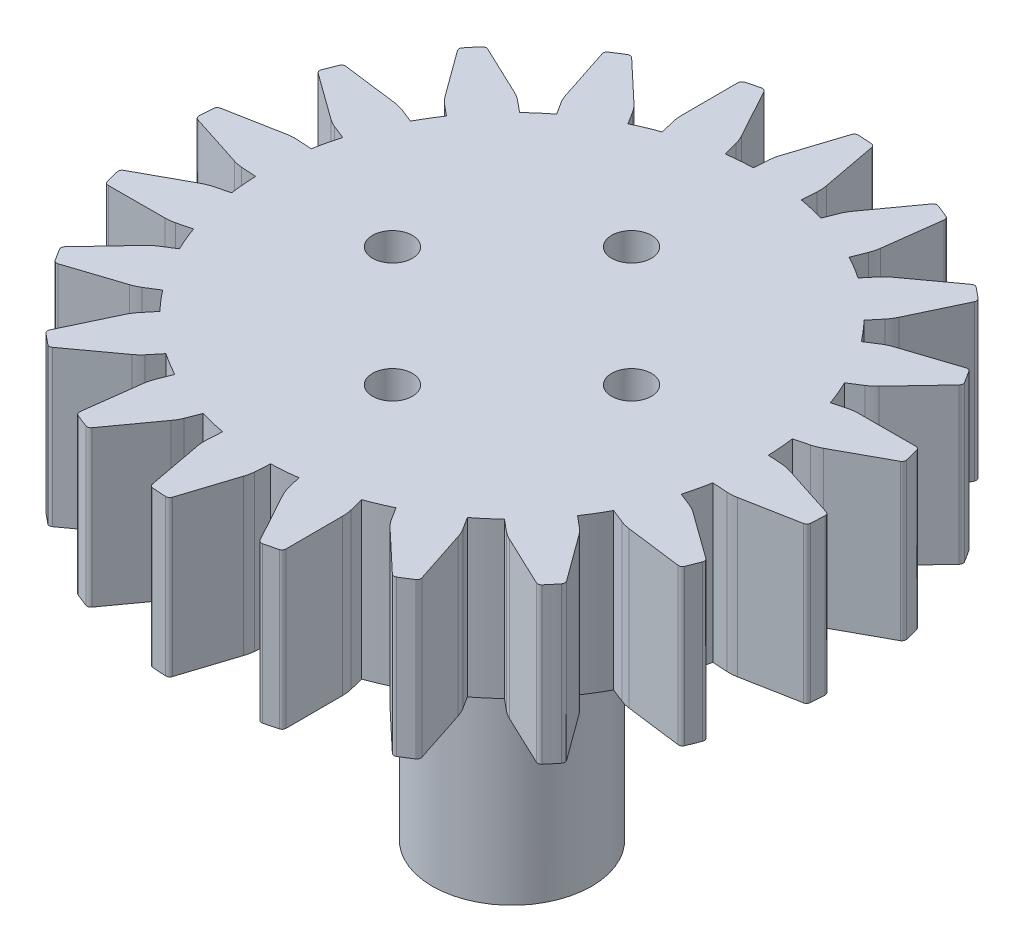
SolidWorks part; units mm, degrees
ref_plane "Front Plane" through (0, 0, 0) normal (0, 0, 1) x (1, 0, 0)
ref_plane "Top Plane" through (0, 0, 0) normal (0, 1, 0) x (1, 0, 0)
ref_plane "Right Plane" through (0, 0, 0) normal (1, 0, 0) x (0, 0, -1)
sketch "Sketch1" plane through (0, 0, 0) normal (0, 1, 0) x (1, 0, 0)
  line L1 (2.0673, 12.6488) -> (2.1144, 13.3972)
  line L2 (2.0838, 13.8927) -> (1.5574, 16.6892)
  line L3 (0.4846, 16.7567) -> (-0.3881, 14.0482)
  line L4 (-0.4814, 13.5905) -> (-0.5285, 12.8421)
  line L11 (5.7598, 11.3604) -> (6.0358, 12.0576)
  line L12 (6.1599, 12.5383) -> (6.5234, 15.3605)
  line L13 (5.524, 15.7563) -> (3.8571, 13.4501)
  line L14 (3.6268, 13.0436) -> (3.3508, 12.3464)
  line L15 (8.8735, 8.994) -> (9.3514, 9.5718)
  line L16 (9.618, 9.9906) -> (10.8358, 12.5624)
  line L17 (10.0076, 13.2476) -> (7.7096, 11.5694)
  line L18 (7.365, 11.2539) -> (6.8871, 10.6762)
  line L19 (11.1035, 5.7812) -> (11.7366, 6.183)
  line L20 (12.1195, 6.499) -> (14.0725, 8.5686)
  line L21 (13.4965, 9.4762) -> (10.7924, 8.5902)
  line L22 (10.3672, 8.3967) -> (9.7341, 7.9949)
  line L23 (12.2315, 2.0366) -> (12.9578, 2.2231)
  line L24 (13.4196, 2.4053) -> (15.9166, 3.77)
  line L25 (15.6492, 4.8112) -> (12.8037, 4.8042)
  line L26 (12.3395, 4.7515) -> (11.6132, 4.5651)
  line L27 (12.1472, -1.8734) -> (12.8956, -1.9204)
  line L28 (13.3911, -1.8899) -> (16.1876, -1.3635)
  line L29 (16.2551, -0.2907) -> (13.5466, 0.582)
  line L30 (13.0889, 0.6753) -> (12.3405, 0.7224)
  line L31 (10.8588, -5.5659) -> (11.556, -5.8419)
  line L32 (12.0367, -5.966) -> (14.8589, -6.3295)
  line L33 (15.2546, -5.3301) -> (12.9485, -3.6631)
  line L34 (12.542, -3.4329) -> (11.8448, -3.1569)
  line L35 (8.4924, -8.6796) -> (9.0702, -9.1575)
  line L36 (9.489, -9.424) -> (12.0608, -10.6419)
  line L37 (12.746, -9.8137) -> (11.0678, -7.5157)
  line L38 (10.7523, -7.1711) -> (10.1745, -6.6931)
  line L39 (5.2796, -10.9096) -> (5.6814, -11.5427)
  line L40 (5.9974, -11.9256) -> (8.0669, -13.8786)
  line L41 (8.9745, -13.3026) -> (8.0886, -10.5985)
  line L42 (7.8951, -10.1733) -> (7.4933, -9.5402)
  line L43 (1.535, -12.0376) -> (1.7215, -12.7639)
  line L44 (1.9037, -13.2257) -> (3.2684, -15.7226)
  line L45 (4.3096, -15.4553) -> (4.3026, -12.6098)
  line L46 (4.2499, -12.1456) -> (4.0635, -11.4193)
  line L47 (-2.375, -11.9533) -> (-2.422, -12.7017)
  line L48 (-2.3915, -13.1972) -> (-1.8651, -15.9936)
  line L49 (-0.7923, -16.0611) -> (0.0804, -13.3527)
  line L50 (0.1737, -12.895) -> (0.2208, -12.1466)
  line L51 (-6.0675, -10.6649) -> (-6.3435, -11.3621)
  line L52 (-6.4676, -11.8428) -> (-6.8311, -14.665)
  line L53 (-5.8317, -15.0607) -> (-4.1648, -12.7546)
  line L54 (-3.9345, -12.348) -> (-3.6585, -11.6509)
  line L55 (-9.1812, -8.2985) -> (-9.6591, -8.8762)
  line L56 (-9.9257, -9.2951) -> (-11.1435, -11.8668)
  line L57 (-10.3153, -12.552) -> (-8.0173, -10.8738)
  line L58 (-7.6727, -10.5584) -> (-7.1948, -9.9806)
  line L59 (-11.4112, -5.0857) -> (-12.0443, -5.4875)
  line L60 (-12.4272, -5.8035) -> (-14.3802, -7.873)
  line L61 (-13.8042, -8.7806) -> (-11.1001, -7.8947)
  line L62 (-10.6749, -7.7011) -> (-10.0418, -7.2994)
  line L63 (-12.5392, -1.3411) -> (-13.2655, -1.5275)
  line L64 (-13.7273, -1.7097) -> (-16.2243, -3.0745)
  line L65 (-15.9569, -4.1157) -> (-13.1114, -4.1087)
  line L66 (-12.6472, -4.056) -> (-11.9209, -3.8695)
  line L67 (-12.4549, 2.5689) -> (-13.2033, 2.616)
  line L68 (-13.6988, 2.5854) -> (-16.4952, 2.059)
  line L69 (-16.5627, 0.9862) -> (-13.8543, 0.1135)
  line L70 (-13.3966, 0.0202) -> (-12.6482, -0.0269)
  line L71 (-11.1665, 6.2614) -> (-11.8637, 6.5374)
  line L72 (-12.3444, 6.6615) -> (-15.1666, 7.0251)
  line L73 (-15.5623, 6.0256) -> (-13.2562, 4.3587)
  line L74 (-12.8497, 4.1285) -> (-12.1525, 3.8524)
  line L75 (-8.8001, 9.3751) -> (-9.3778, 9.853)
  line L76 (-9.7967, 10.1196) -> (-12.3685, 11.3374)
  line L77 (-13.0536, 10.5092) -> (-11.3754, 8.2112)
  line L78 (-11.06, 7.8666) -> (-10.4822, 7.3887)
  line L79 (-5.5873, 11.6051) -> (-5.9891, 12.2382)
  line L80 (-6.3051, 12.6211) -> (-8.3746, 14.5741)
  line L81 (-9.2822, 13.9981) -> (-8.3963, 11.294)
  line L82 (-8.2027, 10.8688) -> (-7.801, 10.2357)
  line L83 (-1.8427, 12.7332) -> (-2.0292, 13.4594)
  line L84 (-2.2114, 13.9213) -> (-3.5761, 16.4182)
  line L85 (-4.6173, 16.1508) -> (-4.6103, 13.3053)
  line L86 (-4.5576, 12.8411) -> (-4.3711, 12.1149)
  arc A1 (3.3508, 12.3464) -> (2.0673, 12.6488) centre (-0.1538, 0.3478) ccw
  arc A2 (-0.5285, 12.8421) -> (-1.8427, 12.7332) centre (-0.1538, 0.3478) ccw
  arc A3 (2.1144, 13.3972) -> (2.0838, 13.8927) centre (0.1183, 13.5228) ccw
  arc A4 (1.5574, 16.6892) -> (1.3769, 16.8515) centre (1.3609, 16.6522) ccw
  arc A5 (1.3769, 16.8515) -> (0.684, 16.8951) centre (-0.2094, -2.8347) ccw
  arc A6 (0.684, 16.8951) -> (0.4846, 16.7567) centre (0.675, 16.6953) ccw
  arc A7 (-0.3881, 14.0482) -> (-0.4814, 13.5905) centre (1.5115, 13.4225) ccw
  arc A8 (-4.3711, 12.1149) -> (-5.5873, 11.6051) centre (-0.1538, 0.3478) ccw
  arc A9 (-7.801, 10.2357) -> (-8.8001, 9.3751) centre (-0.1538, 0.3478) ccw
  arc A10 (-10.4822, 7.3887) -> (-11.1665, 6.2614) centre (-0.1538, 0.3478) ccw
  arc A11 (-12.1525, 3.8524) -> (-12.4549, 2.5689) centre (-0.1538, 0.3478) ccw
  arc A12 (-12.6482, -0.0269) -> (-12.5392, -1.3411) centre (-0.1538, 0.3478) ccw
  arc A14 (-11.9209, -3.8695) -> (-11.4112, -5.0857) centre (-0.1538, 0.3478) ccw
  arc A15 (-10.0418, -7.2994) -> (-9.1812, -8.2985) centre (-0.1538, 0.3478) ccw
  arc A16 (-7.1948, -9.9806) -> (-6.0675, -10.6649) centre (-0.1538, 0.3478) ccw
  arc A17 (-3.6585, -11.6509) -> (-2.375, -11.9533) centre (-0.1538, 0.3478) ccw
  arc A18 (0.2208, -12.1466) -> (1.535, -12.0376) centre (-0.1538, 0.3478) ccw
  arc A19 (6.0358, 12.0576) -> (6.1599, 12.5383) centre (4.1763, 12.7938) ccw
  arc A20 (6.5234, 15.3605) -> (6.402, 15.5707) centre (6.3251, 15.3861) ccw
  arc A21 (6.402, 15.5707) -> (5.7564, 15.8263) centre (-1.1901, -2.6617) ccw
  arc A22 (5.7564, 15.8263) -> (5.524, 15.7563) centre (5.6861, 15.6391) ccw
  arc A23 (3.8571, 13.4501) -> (3.6268, 13.0436) centre (5.4703, 12.268) ccw
  arc A24 (9.3514, 9.5718) -> (9.618, 9.9906) centre (7.8104, 10.8466) ccw
  arc A25 (10.8358, 12.5624) -> (10.7853, 12.7998) centre (10.6551, 12.648) ccw
  arc A26 (10.7853, 12.7998) -> (10.2503, 13.2424) centre (-2.0694, -2.1942) ccw
  arc A27 (10.2503, 13.2424) -> (10.0076, 13.2476) centre (10.1255, 13.0861) ccw
  arc A28 (7.7096, 11.5694) -> (7.365, 11.2539) centre (8.8786, 9.9466) ccw
  arc A29 (11.7366, 6.183) -> (12.1195, 6.499) centre (10.6649, 7.8717) ccw
  arc A30 (14.0725, 8.5686) -> (14.0978, 8.81) centre (13.927, 8.7058) ccw
  arc A31 (14.0978, 8.81) -> (13.7257, 9.3962) centre (-2.7612, -1.4778) ccw
  arc A32 (13.7257, 9.3962) -> (13.4965, 9.4762) centre (13.5588, 9.2861) ccw
  arc A33 (10.7924, 8.5902) -> (10.3672, 8.3967) centre (11.4027, 6.6856) ccw
  arc A34 (12.9578, 2.2231) -> (13.4196, 2.4053) centre (12.4604, 4.1602) ccw
  arc A35 (15.9166, 3.77) -> (16.0152, 3.9918) centre (15.8206, 3.9455) ccw
  arc A36 (16.0152, 3.9918) -> (15.8425, 4.6643) centre (-3.1977, -0.5828) ccw
  arc A37 (15.8425, 4.6643) -> (15.6492, 4.8112) centre (15.6497, 4.6112) ccw
  arc A38 (12.8037, 4.8042) -> (12.3395, 4.7515) centre (12.7956, 2.8042) ccw
  arc A39 (12.8956, -1.9204) -> (13.3911, -1.8899) centre (13.0212, 0.0756) ccw
  arc A40 (16.1876, -1.3635) -> (16.3499, -1.183) centre (16.1506, -1.167) ccw
  arc A41 (16.3499, -1.183) -> (16.3935, -0.4901) centre (-3.3363, 0.4034) ccw
  arc A42 (16.3935, -0.4901) -> (16.2551, -0.2907) centre (16.1937, -0.4811) ccw
  arc A43 (13.5466, 0.582) -> (13.0889, 0.6753) centre (12.9209, -1.3176) ccw
  arc A44 (11.556, -5.8419) -> (12.0367, -5.966) centre (12.2922, -3.9824) ccw
  arc A45 (14.8589, -6.3295) -> (15.0691, -6.208) centre (14.8845, -6.1312) ccw
  arc A46 (15.0691, -6.208) -> (15.3247, -5.5625) centre (-3.1633, 1.3841) ccw
  arc A47 (15.3247, -5.5625) -> (15.2546, -5.3301) centre (15.1375, -5.4922) ccw
  arc A48 (12.9485, -3.6631) -> (12.542, -3.4329) centre (11.7664, -5.2764) ccw
  arc A49 (9.0702, -9.1575) -> (9.489, -9.424) centre (10.345, -7.6165) ccw
  arc A50 (12.0608, -10.6419) -> (12.2982, -10.5913) centre (12.1464, -10.4612) ccw
  arc A51 (12.2982, -10.5913) -> (12.7408, -10.0564) centre (-2.6958, 2.2633) ccw
  arc A52 (12.7408, -10.0564) -> (12.746, -9.8137) centre (12.5844, -9.9316) ccw
  arc A53 (11.0678, -7.5157) -> (10.7523, -7.1711) centre (9.445, -8.6847) ccw
  arc A54 (5.6814, -11.5427) -> (5.9974, -11.9256) centre (7.3701, -10.471) ccw
  arc A55 (8.0669, -13.8786) -> (8.3084, -13.9038) centre (8.2042, -13.7331) ccw
  arc A56 (8.3084, -13.9038) -> (8.8946, -13.5318) centre (-1.9795, 2.9551) ccw
  arc A57 (8.8946, -13.5318) -> (8.9745, -13.3026) centre (8.7845, -13.3649) ccw
  arc A58 (8.0886, -10.5985) -> (7.8951, -10.1733) centre (6.184, -11.2088) ccw
  arc A59 (1.7215, -12.7639) -> (1.9037, -13.2257) centre (3.6586, -12.2665) ccw
  arc A60 (3.2684, -15.7226) -> (3.4902, -15.8213) centre (3.4439, -15.6267) ccw
  arc A61 (3.4902, -15.8213) -> (4.1627, -15.6486) centre (-1.0844, 3.3916) ccw
  arc A62 (4.1627, -15.6486) -> (4.3096, -15.4553) centre (4.1096, -15.4558) ccw
  arc A63 (4.3026, -12.6098) -> (4.2499, -12.1456) centre (2.3026, -12.6017) ccw
  arc A64 (-2.422, -12.7017) -> (-2.3915, -13.1972) centre (-0.426, -12.8272) ccw
  arc A65 (-1.8651, -15.9936) -> (-1.6846, -16.156) centre (-1.6686, -15.9566) ccw
  arc A66 (-1.6846, -16.156) -> (-0.9917, -16.1996) centre (-0.0982, 3.5302) ccw
  arc A67 (-0.9917, -16.1996) -> (-0.7923, -16.0611) centre (-0.9827, -15.9998) ccw
  arc A68 (0.0804, -13.3527) -> (0.1737, -12.895) centre (-1.8192, -12.727) ccw
  arc A69 (-6.3435, -11.3621) -> (-6.4676, -11.8428) centre (-4.484, -12.0983) ccw
  arc A70 (-6.8311, -14.665) -> (-6.7097, -14.8752) centre (-6.6328, -14.6906) ccw
  arc A71 (-6.7097, -14.8752) -> (-6.0641, -15.1308) centre (0.8825, 3.3573) ccw
  arc A72 (-6.0641, -15.1308) -> (-5.8317, -15.0607) centre (-5.9938, -14.9436) ccw
  arc A73 (-4.1648, -12.7546) -> (-3.9345, -12.348) centre (-5.778, -11.5725) ccw
  arc A74 (-9.6591, -8.8762) -> (-9.9257, -9.2951) centre (-8.1181, -10.1511) ccw
  arc A75 (-11.1435, -11.8668) -> (-11.0929, -12.1043) centre (-10.9628, -11.9524) ccw
  arc A76 (-11.0929, -12.1043) -> (-10.558, -12.5468) centre (1.7617, 2.8897) ccw
  arc A77 (-10.558, -12.5468) -> (-10.3153, -12.552) centre (-10.4332, -12.3905) ccw
  arc A78 (-8.0173, -10.8738) -> (-7.6727, -10.5584) centre (-9.1863, -9.2511) ccw
  arc A79 (-12.0443, -5.4875) -> (-12.4272, -5.8035) centre (-10.9726, -7.1761) ccw
  arc A80 (-14.3802, -7.873) -> (-14.4054, -8.1145) centre (-14.2347, -8.0103) ccw
  arc A81 (-14.4054, -8.1145) -> (-14.0334, -8.7007) centre (2.4535, 2.1734) ccw
  arc A82 (-14.0334, -8.7007) -> (-13.8042, -8.7806) centre (-13.8665, -8.5906) ccw
  arc A83 (-11.1001, -7.8947) -> (-10.6749, -7.7011) centre (-11.7104, -5.9901) ccw
  arc A84 (-13.2655, -1.5275) -> (-13.7273, -1.7097) centre (-12.7681, -3.4647) ccw
  arc A85 (-16.2243, -3.0745) -> (-16.3229, -3.2963) centre (-16.1283, -3.25) ccw
  arc A86 (-16.3229, -3.2963) -> (-16.1502, -3.9688) centre (2.89, 1.2783) ccw
  arc A87 (-16.1502, -3.9688) -> (-15.9569, -4.1157) centre (-15.9574, -3.9157) ccw
  arc A88 (-13.1114, -4.1087) -> (-12.6472, -4.056) centre (-13.1033, -2.1087) ccw
  arc A89 (-13.2033, 2.616) -> (-13.6988, 2.5854) centre (-13.3289, 0.6199) ccw
  arc A90 (-16.4952, 2.059) -> (-16.6576, 1.8786) centre (-16.4582, 1.8625) ccw
  arc A91 (-16.6576, 1.8786) -> (-16.7012, 1.1856) centre (3.0286, 0.2922) ccw
  arc A92 (-16.7012, 1.1856) -> (-16.5627, 0.9862) centre (-16.5014, 1.1766) ccw
  arc A93 (-13.8543, 0.1135) -> (-13.3966, 0.0202) centre (-13.2286, 2.0131) ccw
  arc A94 (-11.8637, 6.5374) -> (-12.3444, 6.6615) centre (-12.5999, 4.6779) ccw
  arc A95 (-15.1666, 7.0251) -> (-15.3768, 6.9036) centre (-15.1922, 6.8267) ccw
  arc A96 (-15.3768, 6.9036) -> (-15.6324, 6.258) centre (2.8556, -0.6885) ccw
  arc A97 (-15.6324, 6.258) -> (-15.5623, 6.0256) centre (-15.4452, 6.1877) ccw
  arc A98 (-13.2562, 4.3587) -> (-12.8497, 4.1285) centre (-12.0741, 5.9719) ccw
  arc A99 (-9.3778, 9.853) -> (-9.7967, 10.1196) centre (-10.6527, 8.312) ccw
  arc A100 (-12.3685, 11.3374) -> (-12.6059, 11.2869) centre (-12.4541, 11.1567) ccw
  arc A101 (-12.6059, 11.2869) -> (-13.0484, 10.7519) centre (2.3881, -1.5678) ccw
  arc A102 (-13.0484, 10.7519) -> (-13.0536, 10.5092) centre (-12.8921, 10.6271) ccw
  arc A103 (-11.3754, 8.2112) -> (-11.06, 7.8666) centre (-9.7527, 9.3802) ccw
  arc A104 (-5.9891, 12.2382) -> (-6.3051, 12.6211) centre (-7.6778, 11.1665) ccw
  arc A105 (-8.3746, 14.5741) -> (-8.6161, 14.5994) centre (-8.5119, 14.4286) ccw
  arc A106 (-8.6161, 14.5994) -> (-9.2023, 14.2273) centre (1.6718, -2.2596) ccw
  arc A107 (-9.2023, 14.2273) -> (-9.2822, 13.9981) centre (-9.0922, 14.0604) ccw
  arc A108 (-8.3963, 11.294) -> (-8.2027, 10.8688) centre (-6.4917, 11.9043) ccw
  arc A109 (-2.0292, 13.4594) -> (-2.2114, 13.9213) centre (-3.9663, 12.962) ccw
  arc A110 (-3.5761, 16.4182) -> (-3.7979, 16.5168) centre (-3.7516, 16.3223) ccw
  arc A111 (-3.7979, 16.5168) -> (-4.4704, 16.3441) centre (0.7767, -2.6961) ccw
  arc A112 (-4.4704, 16.3441) -> (-4.6173, 16.1508) centre (-4.4173, 16.1513) ccw
  arc A113 (-4.6103, 13.3053) -> (-4.5576, 12.8411) centre (-2.6103, 13.2972) ccw
  arc A114 (4.0635, -11.4193) -> (5.2796, -10.9096) centre (-0.1538, 0.3478) ccw
  arc A115 (7.4933, -9.5402) -> (8.4924, -8.6796) centre (-0.1538, 0.3478) ccw
  arc A116 (10.1745, -6.6931) -> (10.8588, -5.5659) centre (-0.1538, 0.3478) ccw
  arc A117 (11.8448, -3.1569) -> (12.1472, -1.8734) centre (-0.1538, 0.3478) ccw
  arc A118 (6.8871, 10.6762) -> (5.7598, 11.3604) centre (-0.1538, 0.3478) ccw
  arc A119 (9.7341, 7.9949) -> (8.8735, 8.994) centre (-0.1538, 0.3478) ccw
  arc A120 (11.6132, 4.5651) -> (11.1035, 5.7812) centre (-0.1538, 0.3478) ccw
  arc A121 (12.3405, 0.7224) -> (12.2315, 2.0366) centre (-0.1538, 0.3478) ccw
  circle A122 centre (-0.1538, 0.3478) radius 1.934
  point P337 (-0.1538, 0.3478)
  dimension "D1" = 25
  dimension "D2" = 20
extrude "Boss-Extrude1" add sketch "Sketch1" along normal blind 7.8
sketch "Sketch4" plane through (0, 7.8, 0) normal (0, 1, 0) x (1, 0, 0)
  line L0 (-0.1538, 6.3478) -> (-0.1538, 5.3478)
  line L1 (-0.1538, -4.6522) -> (-0.1538, -5.6522)
  circle A0 centre (-0.1538, 6.3478) radius 1
  circle A1 centre (-0.1538, -5.6522) radius 1
  circle A2 centre (5.8462, 0.3478) radius 1
  circle A4 centre (-6.1538, 0.3478) radius 1
  point P3 (-0.1538, 0.3478)
  point P5 (-0.1538, 7.3478)
  point P6 (-0.1538, 11.5978)
  point P15 (-0.1538, 0.3478)
  dimension "D1" = 2
  dimension "D2" = 2
  dimension "D3" = 12
extrude "Cut-Extrude1" cut sketch "Sketch4" against normal blind 10
sketch "Sketch5" plane through (0, 0, 0) normal (0, -1, 0) x (1, 0, 0)
  circle A0 centre (-0.1538, -0.3478) radius 4
  dimension "D1" = 8
extrude "Boss-Extrude2" add sketch "Sketch5" along normal blind 15
sketch "Sketch6" plane through (0, 7.8, 0) normal (0, 1, 0) x (1, 0, 0)
  circle A1 centre (-0.1538, 0.3478) radius 1.934
  circle A2 centre (-0.1538, 0.3478) radius 1.934
  dimension "D1" = 0
extrude "Boss-Extrude3" add sketch "Sketch6" against normal blind 20
